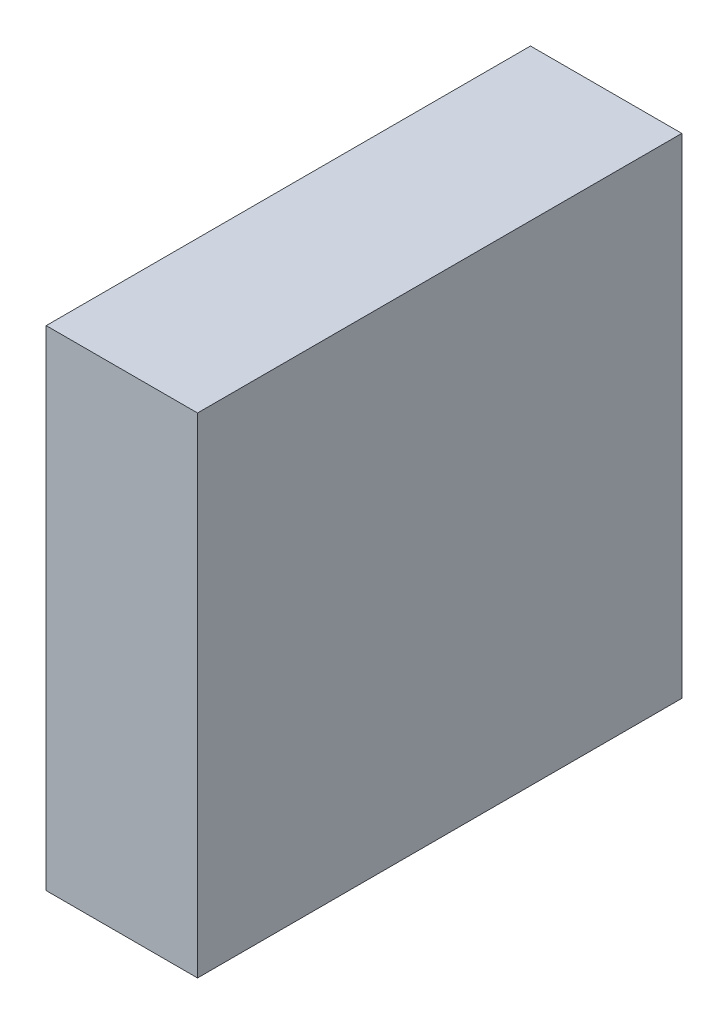
SolidWorks part; units mm, degrees
ref_plane "Plan de face" through (0, 0, 0) normal (0, 0, 1) x (1, 0, 0)
ref_plane "Plan de dessus" through (0, 0, 0) normal (0, 1, 0) x (1, 0, 0)
ref_plane "Plan de droite" through (0, 0, 0) normal (1, 0, 0) x (0, 0, -1)
sketch "Esquisse1" plane through (0, 0, 0) normal (1, 0, 0) x (0, 0, -1)
  line L1 (-48, -48.5) -> (48, -48.5)
  line L2 (-48, -48.5) -> (-48, 48.5)
  line L3 (-48, 48.5) -> (48, 48.5)
  line L4 (48, -48.5) -> (48, 48.5)
  line L5 (-48, -48.5) -> (48, 48.5) construction
  line L6 (-48, 48.5) -> (48, -48.5) construction
  point P0 (0, 0)
extrude "Boss.-Extru.1" add sketch "Esquisse1" along normal blind 30
